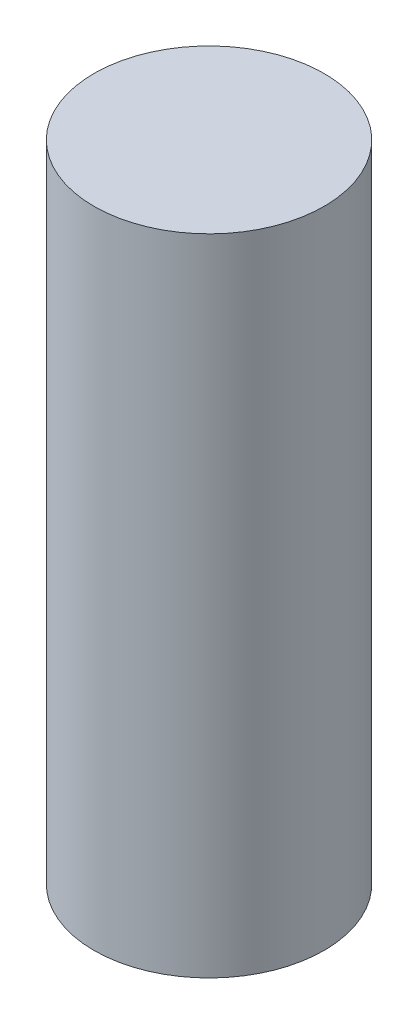
SolidWorks part; units mm, degrees
ref_plane "Front Plane" through (0, 0, 0) normal (0, 0, 1) x (1, 0, 0)
ref_plane "Top Plane" through (0, 0, 0) normal (0, 1, 0) x (1, 0, 0)
ref_plane "Right Plane" through (0, 0, 0) normal (1, 0, 0) x (0, 0, -1)
sketch "Sketch1" plane through (0, 0, 0) normal (0, 1, 0) x (1, 0, 0)
  circle A0 centre (0, 0) radius 3.175
  dimension "D1" = 6.35
extrude "Boss-Extrude1" add sketch "Sketch1" along normal blind 17.78
